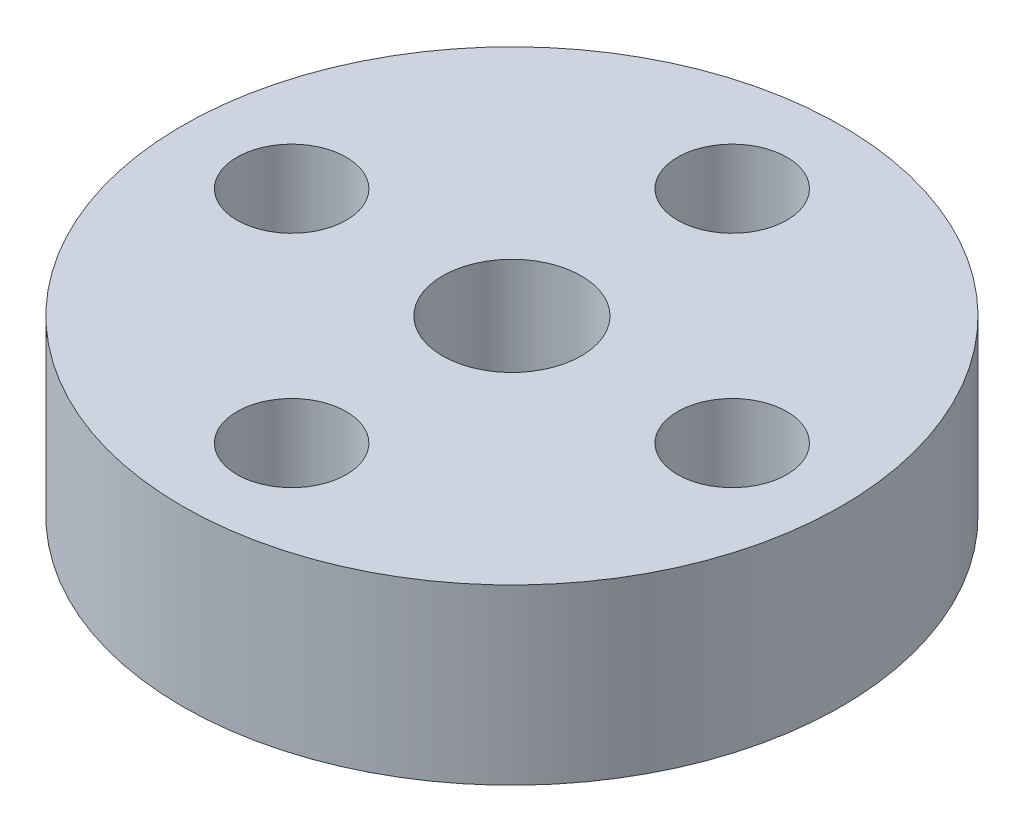
SolidWorks part; units mm, degrees
ref_plane "Front Plane" through (0, 0, 0) normal (0, 0, 1) x (1, 0, 0)
ref_plane "Top Plane" through (0, 0, 0) normal (0, 1, 0) x (1, 0, 0)
ref_plane "Right Plane" through (0, 0, 0) normal (1, 0, 0) x (0, 0, -1)
sketch "Sketch1" plane through (0, 0, 0) normal (0, 1, 0) x (1, 0, 0)
  circle A0 centre (0, 0) radius 9.5
  dimension "D1" = 19
extrude "Boss-Extrude1" add sketch "Sketch1" along normal blind 5
sketch "Sketch2" plane through (0, 5, 0) normal (0, 1, 0) x (1, 0, 0)
  line L0 (0, 6.35) -> (0, -6.35) construction
  line L1 (-6.35, 0) -> (6.35, 0) construction
  circle A0 centre (0, 6.35) radius 1.575
  circle A1 centre (6.35, 0) radius 1.575
  circle A2 centre (0, -6.35) radius 1.575
  circle A3 centre (-6.35, 0) radius 1.575
  circle A4 centre (0, 0) radius 2
  dimension "D1" = 4
  dimension "D2" = 3.15
  dimension "D3" = 6.35
extrude "Cut-Extrude1" cut sketch "Sketch2" against normal up to surface (5 mm away) up to face at (0, 0, 9.5)
